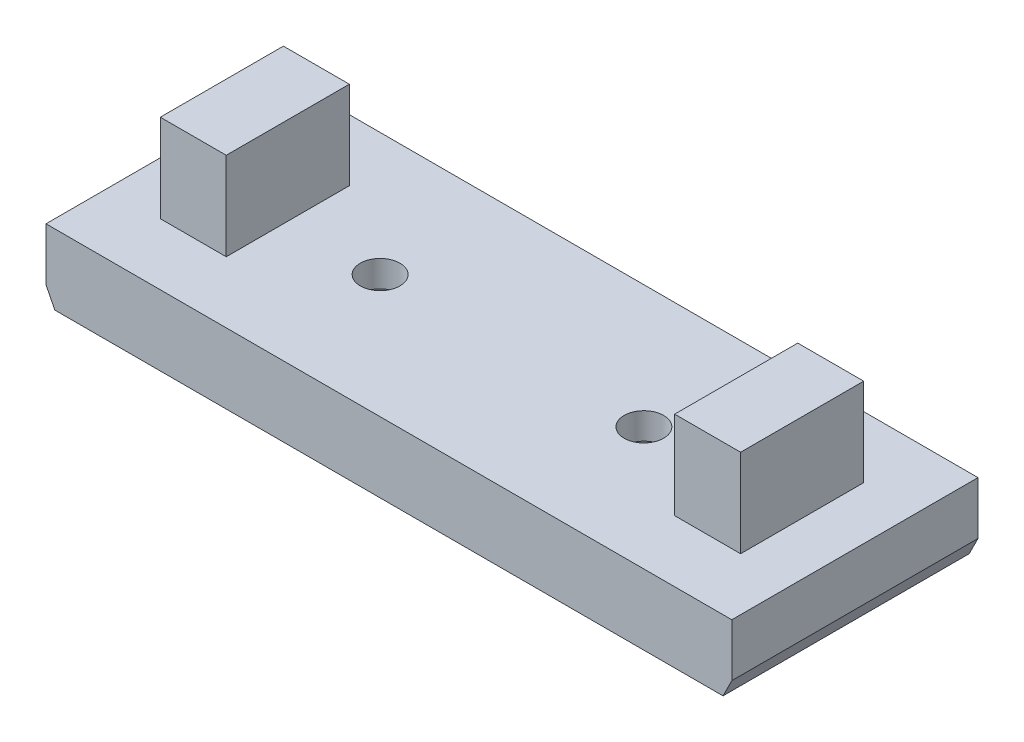
SolidWorks part; units mm, degrees
ref_plane "정면" through (0, 0, 0) normal (0, 0, 1) x (1, 0, 0)
ref_plane "윗면" through (0, 0, 0) normal (0, 1, 0) x (1, 0, 0)
ref_plane "우측면" through (0, 0, 0) normal (1, 0, 0) x (0, 0, -1)
sketch "스케치1" plane through (0, 0, 0) normal (0, 1, 0) x (1, 0, 0)
  line L1 (-19.5, 7) -> (19.5, 7)
  line L2 (-19.5, 7) -> (-19.5, -7)
  line L3 (-19.5, -7) -> (19.5, -7)
  line L4 (19.5, 7) -> (19.5, -7)
  point P4 (19.5, 0)
  point P6 (0, 7)
  dimension "D1" = 39
  dimension "D2" = 14
extrude "보스-돌출1" add sketch "스케치1" along normal blind 4
sketch "스케치2" plane through (0, 0, 0) normal (0, -1, 0) x (1, 0, 0)
  line L7 (10.0115, 0) -> (8.7557, 2.175)
  line L8 (8.7557, 2.175) -> (6.2443, 2.175)
  line L9 (6.2443, 2.175) -> (4.9885, 0)
  line L10 (4.9885, 0) -> (6.2443, -2.175)
  line L11 (6.2443, -2.175) -> (8.7557, -2.175)
  line L12 (8.7557, -2.175) -> (10.0115, 0)
  line L13 (-4.9885, 0) -> (-6.2443, 2.175)
  line L14 (-6.2443, 2.175) -> (-8.7557, 2.175)
  line L15 (-8.7557, 2.175) -> (-10.0115, 0)
  line L16 (-10.0115, 0) -> (-8.7557, -2.175)
  line L17 (-8.7557, -2.175) -> (-6.2443, -2.175)
  line L18 (-6.2443, -2.175) -> (-4.9885, 0)
  circle A1 centre (7.5, 0) radius 2.175 construction
  circle A2 centre (-7.5, 0) radius 2.175 construction
  point P0 (-7.206, 0)
  dimension "D1" = 4.35
  dimension "D2" = 7.5
  dimension "D3" = 7.5
extrude "컷-돌출1" cut sketch "스케치2" against normal offset from surface (2.5 mm away) 1.5 up to face at (0, 4, 0)
sketch "스케치3" plane through (0, 0, 0) normal (0, -1, 0) x (1, 0, 0)
  circle A0 centre (-7.5, 0) radius 1.125
  circle A1 centre (7.5, 0) radius 1.125
  point P4 (0, 0)
  point P5 (-7.5154, 0)
  point P7 (0, 0)
  point P8 (7.5, 0)
  dimension "D1" = 2.25
  dimension "D2" = 7.5
  dimension "D3" = 7.5
extrude "컷-돌출2" cut sketch "스케치3" against normal up to surface (4 mm away) up to face at (0, 4, 0)
sketch "스케치4" plane through (0, 4, 0) normal (0, 1, 0) x (1, 0, 0)
  line L0 (-19.5, 7) -> (-19.5, -7) construction
  line L1 (-12.75, 3.5) -> (-16.5, 3.5)
  line L2 (-12.75, 3.5) -> (-12.75, -3.5)
  line L3 (-12.75, -3.5) -> (-16.5, -3.5)
  line L4 (-16.5, 3.5) -> (-16.5, -3.5)
  line L5 (12.75, 3.5) -> (16.5, 3.5)
  line L6 (12.75, 3.5) -> (12.75, -3.5)
  line L7 (12.75, -3.5) -> (16.5, -3.5)
  line L8 (16.5, 3.5) -> (16.5, -3.5)
  line L9 (19.5, -7) -> (19.5, 7) construction
  point P13 (-12.75, 0)
  point P14 (12.75, 0)
  dimension "D1" = 7
  dimension "D2" = 12.75
  dimension "D3" = 12.75
  dimension "D4" = 3
  dimension "D5" = 3
  dimension "D6" = 7
extrude "보스-돌출2" add sketch "스케치4" along normal blind 5
sketch "스케치5" plane through (0, 0, 7) normal (0, 0, 1) x (1, 0, 0)
  line L0 (-19.5, 1) -> (-19, 0)
  line L1 (-19.5, 4) -> (-19.5, 0) construction
  line L2 (-19.5, 0) -> (19.5, 0) construction
  line L3 (-19, 0) -> (-19.5, 0)
  line L4 (-19.5, 0) -> (-19.5, 1)
  line L5 (19.5, 1) -> (19.5, 0)
  line L6 (19.5, 4) -> (19.5, 0) construction
  line L7 (19.5, 0) -> (19, 0)
  line L8 (19, 0) -> (19.5, 1)
  dimension "D1" = 0.5
  dimension "D2" = 0.5
  dimension "D3" = 1
  dimension "D4" = 1
extrude "컷-돌출4" cut sketch "스케치5" against normal up to surface (14 mm away) up to face at (0, 2, -7)
